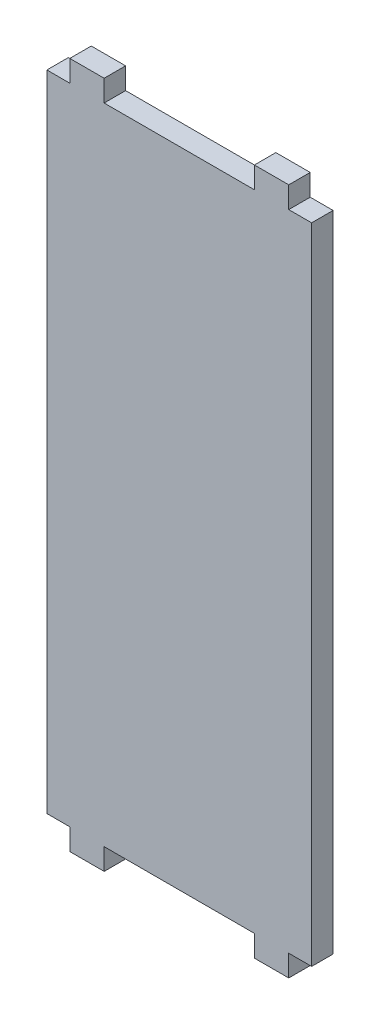
SolidWorks part; units mm, degrees
ref_plane "Front Plane" through (0, 0, 0) normal (0, 0, 1) x (1, 0, 0)
ref_plane "Top Plane" through (0, 0, 0) normal (0, 1, 0) x (1, 0, 0)
ref_plane "Right Plane" through (0, 0, 0) normal (1, 0, 0) x (0, 0, -1)
sketch "Sketch1" plane through (0, 0, 0) normal (0, 0, 1) x (1, 0, 0)
  line L1 (4.7625, -4.7625) -> (-58.7375, -4.7625)
  line L2 (4.7625, -4.7625) -> (4.7625, 147.6375)
  line L3 (4.7625, 147.6375) -> (-58.7375, 147.6375)
  line L4 (-58.7375, -4.7625) -> (-58.7375, 147.6375)
  line L5 (-5.08, -4.7625) -> (-12.7, -4.7625)
  line L6 (-5.08, -4.7625) -> (-5.08, 0)
  line L7 (-5.08, 0) -> (-12.7, 0)
  line L8 (-12.7, -4.7625) -> (-12.7, 0)
  line L9 (-46.0375, -4.7625) -> (-53.6575, -4.7625)
  line L10 (-46.0375, -4.7625) -> (-46.0375, 0)
  line L11 (-46.0375, 0) -> (-53.6575, 0)
  line L12 (-53.6575, -4.7625) -> (-53.6575, 0)
  line L13 (-5.08, 147.6375) -> (-12.7, 147.6375)
  line L14 (-5.08, 147.6375) -> (-5.08, 142.875)
  line L15 (-5.08, 142.875) -> (-12.7, 142.875)
  line L16 (-12.7, 147.6375) -> (-12.7, 142.875)
  line L17 (-46.0375, 142.875) -> (-53.6575, 142.875)
  line L18 (-46.0375, 142.875) -> (-46.0375, 147.6375)
  line L19 (-46.0375, 147.6375) -> (-53.6575, 147.6375)
  line L20 (-53.6575, 142.875) -> (-53.6575, 147.6375)
  line L21 (0, 0) -> (-58.7375, 0)
  line L22 (0, 0) -> (0, 142.875)
  line L23 (0, 142.875) -> (-58.7375, 142.875)
  line L24 (-58.7375, 0) -> (-58.7375, 142.875)
extrude "Boss-Extrude1" add sketch "Sketch1" along normal blind 4.7625 contours L22 L23 L15 L17 L4 L21 L11 L7 | L3 L16 L15 L14 | L20 L17 L18 L3 | L8 L1 L6 L7
